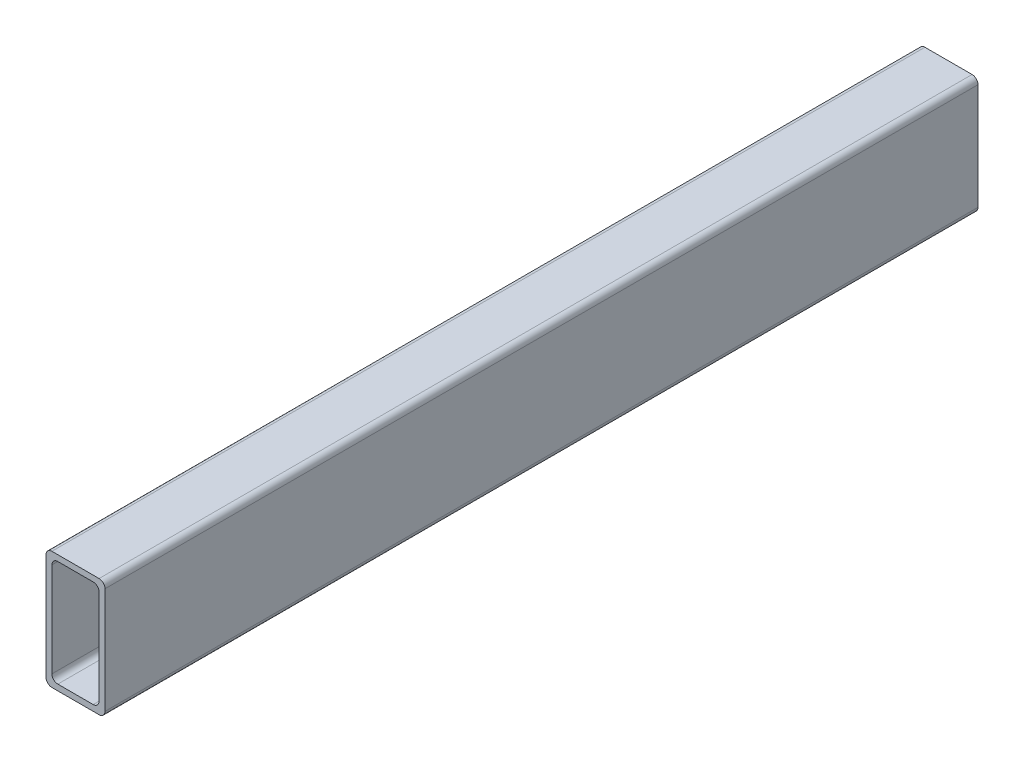
SolidWorks part; units mm, degrees
ref_plane "Спереди" through (0, 0, 0) normal (0, 0, 1) x (1, 0, 0)
ref_plane "Сверху" through (0, 0, 0) normal (0, 1, 0) x (1, 0, 0)
ref_plane "Справа" through (0, 0, 0) normal (1, 0, 0) x (0, 0, -1)
sketch "Эскиз1" plane through (0, 0, 0) normal (0, 0, 1) x (1, 0, 0)
  line L0 (-10, 50) -> (10, 50)
  line L1 (12.5, 47.5) -> (12.5, 2.5)
  line L2 (10, 0) -> (-10, 0)
  line L3 (-12.5, 2.5) -> (-12.5, 47.5)
  line L4 (-7.5, 47.5) -> (7.5, 47.5)
  line L5 (10, 45) -> (10, 5)
  line L6 (7.5, 2.5) -> (-7.5, 2.5)
  line L7 (-10, 5) -> (-10, 45)
  arc A0 (12.5, 47.5) -> (10, 50) centre (10, 47.5) ccw
  arc A1 (10, 0) -> (12.5, 2.5) centre (10, 2.5) ccw
  arc A2 (-12.5, 2.5) -> (-10, 0) centre (-10, 2.5) ccw
  arc A3 (-10, 50) -> (-12.5, 47.5) centre (-10, 47.5) ccw
  arc A4 (10, 45) -> (7.5, 47.5) centre (7.5, 45) ccw
  arc A5 (7.5, 2.5) -> (10, 5) centre (7.5, 5) ccw
  arc A6 (-10, 5) -> (-7.5, 2.5) centre (-7.5, 5) ccw
  arc A7 (-7.5, 47.5) -> (-10, 45) centre (-7.5, 45) ccw
extrude "Бобышка-Вытянуть1" add sketch "Эскиз1" against normal blind 370
